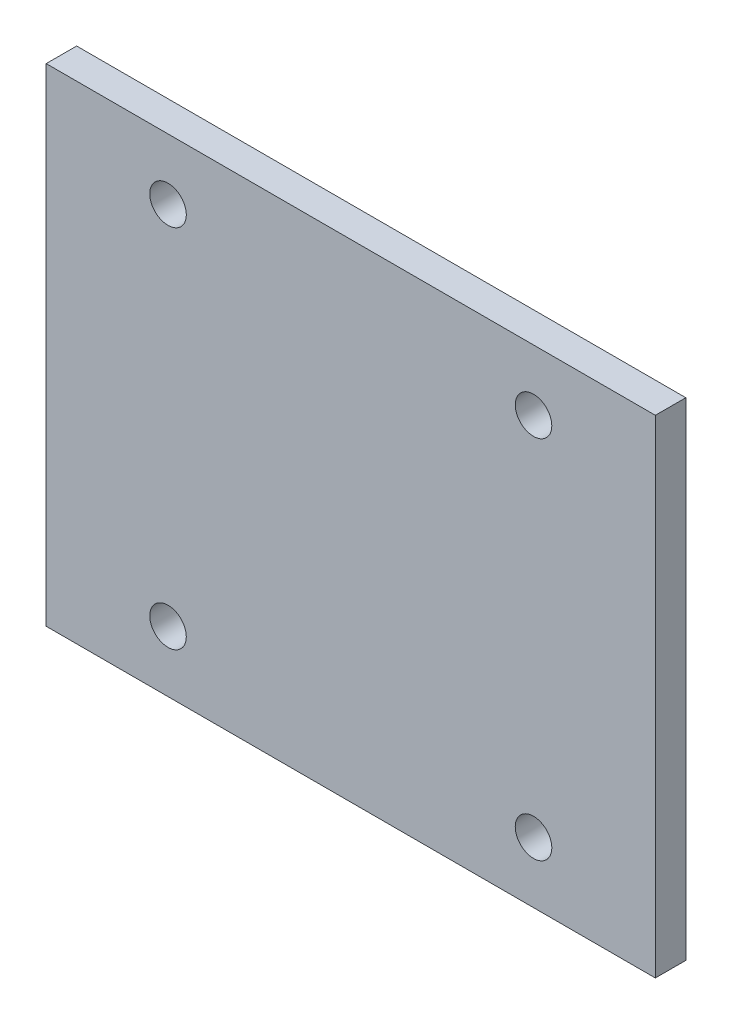
SolidWorks part; units mm, degrees
ref_plane "Front Plane" through (0, 0, 0) normal (0, 0, 1) x (1, 0, 0)
ref_plane "Top Plane" through (0, 0, 0) normal (0, 1, 0) x (1, 0, 0)
ref_plane "Right Plane" through (0, 0, 0) normal (1, 0, 0) x (0, 0, -1)
sketch "Sketch1" plane through (0, 0, 0) normal (0, 0, 1) x (1, 0, 0)
  line L1 (-25, -20) -> (25, -20)
  line L2 (-25, -20) -> (-25, 20)
  line L3 (-25, 20) -> (25, 20)
  line L4 (25, -20) -> (25, 20)
  line L5 (-25, -20) -> (25, 20) construction
  line L6 (-25, 20) -> (25, -20) construction
  point P0 (0, 0)
  dimension "D1" = 50
  dimension "D2" = 40
extrude "Boss-Extrude1" add sketch "Sketch1" along normal blind 2.5
sketch "Sketch2" plane through (0, 0, 2.5) normal (0, 0, 1) x (1, 0, 0)
  line L0 (0, 0) -> (0, 15) construction
  line L1 (0, 15) -> (15, 15) construction
  line L2 (-25, 0) -> (25, 0) construction
  line L3 (-25, 20) -> (-25, -20) construction
  line L4 (25, -20) -> (25, 20) construction
  circle A0 centre (15, 15) radius 1.5
  circle A1 centre (15, -15) radius 1.5
  circle A2 centre (-15, -15) radius 1.5
  circle A3 centre (-15, 15) radius 1.5
  dimension "D3" = 3
  dimension "D1" = 15
  dimension "D2" = 15
extrude "Cut-Extrude1" cut sketch "Sketch2" against normal blind 2.5
